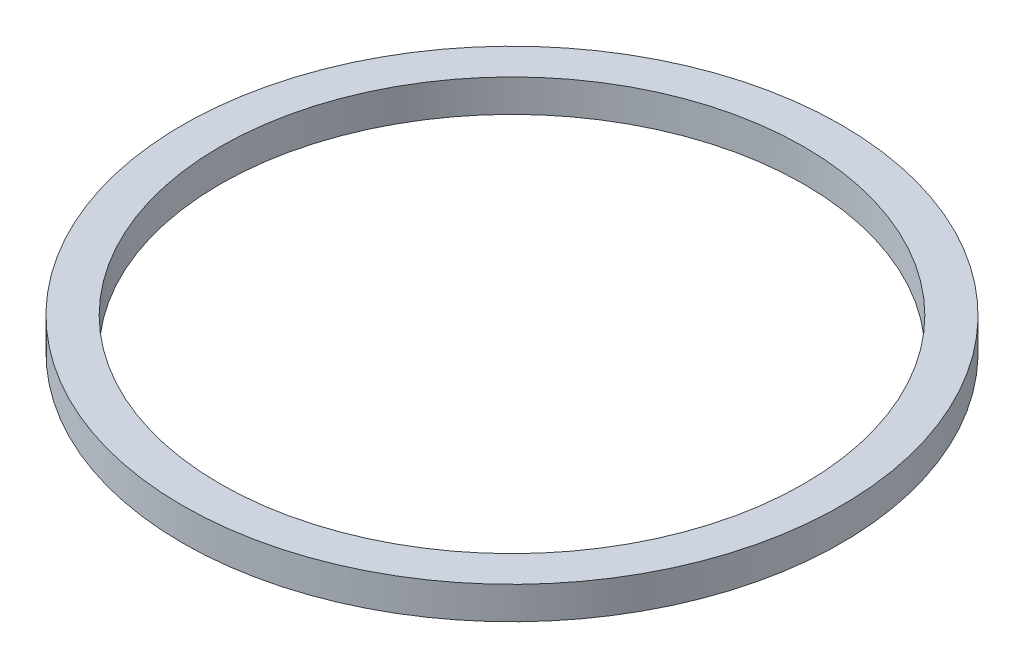
SolidWorks part; units mm, degrees
ref_plane "前视基准面" through (0, 0, 0) normal (0, 0, 1) x (1, 0, 0)
ref_plane "上视基准面" through (0, 0, 0) normal (0, 1, 0) x (1, 0, 0)
ref_plane "右视基准面" through (0, 0, 0) normal (1, 0, 0) x (0, 0, -1)
sketch "草图1" plane through (0, 0, 0) normal (0, 0, 1) x (1, 0, 0)
  line L0 (0, 77.1441) -> (0, -87.8701) construction
  line L1 (-61.6053, 0) -> (62.4304, 0) construction
  line L2 (22.5, 0) -> (22.5, 2.5)
  line L3 (25.4, 0) -> (25.4, 2.5)
  line L4 (22.5, 2.5) -> (25.4, 2.5)
  line L5 (22.5, 0) -> (25.4, 0)
  dimension "D1" = 22.5
  dimension "D2" = 25.4
  dimension "D3" = 2.5
revolve "旋转1" add sketch "草图1" angle 360 about L0
cosmetic thread "装饰螺纹线1" parameters "D2"=46
